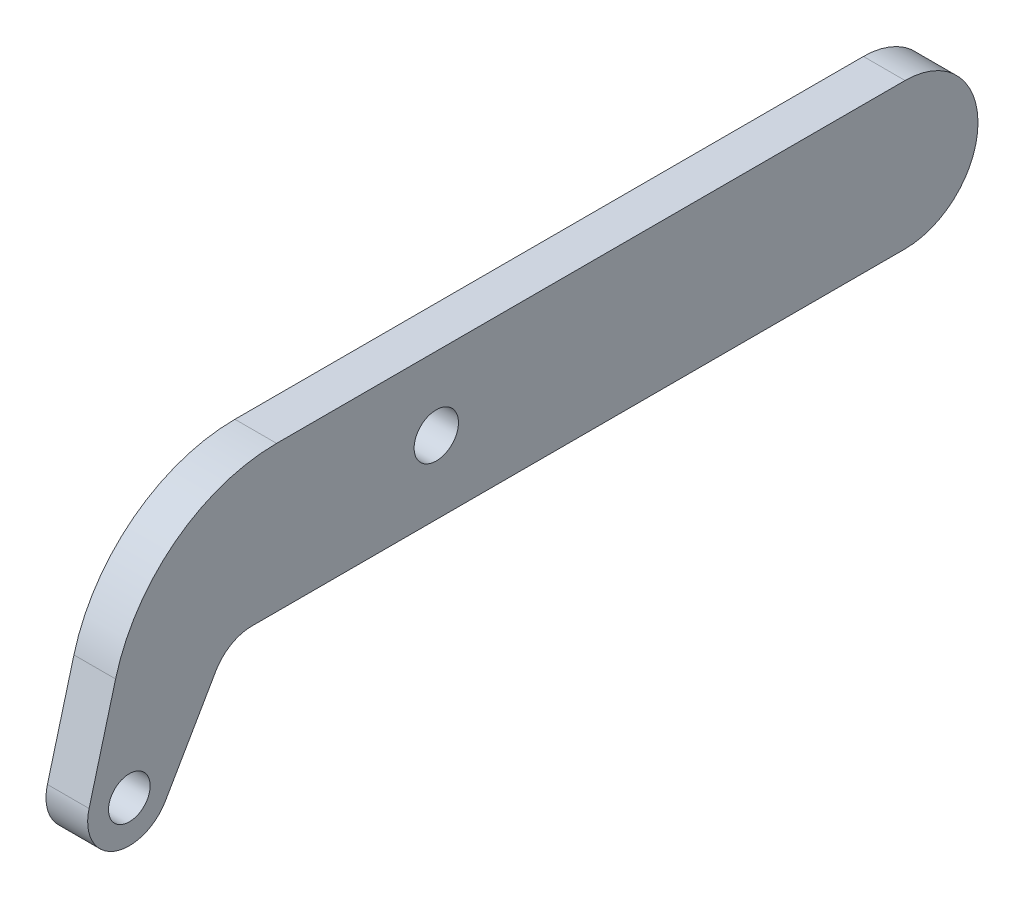
SolidWorks part; units mm, degrees
material "6061-T6 (SS)"
ref_plane "Front Plane" through (0, 0, 0) normal (0, 0, 1) x (1, 0, 0)
ref_plane "Top Plane" through (0, 0, 0) normal (0, 1, 0) x (1, 0, 0)
ref_plane "Right Plane" through (0, 0, 0) normal (1, 0, 0) x (0, 0, -1)
sketch "Sketch1" plane through (0, 0, 0) normal (1, 0, 0) x (0, 0, -1)
  line L0 (3.6662, 0) -> (103.1875, 0)
  line L1 (103.1875, 22.225) -> (7.4168, 22.225)
  line L2 (-1.8331, -3.175) -> (-9.525, -16.4978)
  line L3 (-21.1579, -11.6793) -> (-17.1177, 3.399)
  arc A0 (103.1875, 0) -> (103.1875, 22.225) centre (103.1875, 11.1125) ccw
  arc A2 (-9.525, -16.4978) -> (-21.1579, -11.6793) centre (-15.0243, -13.3228) cw
  arc A3 (7.4168, 22.225) -> (-17.1177, 3.399) centre (7.4168, -3.175) ccw
  arc A4 (-1.8331, -3.175) -> (3.6662, 0) centre (3.6662, -6.35) cw
  circle A5 centre (-15.0243, -13.3228) radius 3.175
  circle A6 centre (31.75, 11.1125) radius 3.3782
  point P17 (0, 0)
  dimension "D5" = 6.35
  dimension "D6" = 15
  dimension "D7" = 25.4
  dimension "D8" = 6.35
  dimension "D9" = 6.35
  dimension "D10" = 6.7564
  dimension "D12" = 11.1125
  dimension "D1" = 22.225
  dimension "D2" = 114.3
  dimension "D3" = 60
  dimension "D4" = 19.05
  dimension "D11" = 31.75
extrude "Boss-Extrude1" add sketch "Sketch1" along normal blind 6.35
